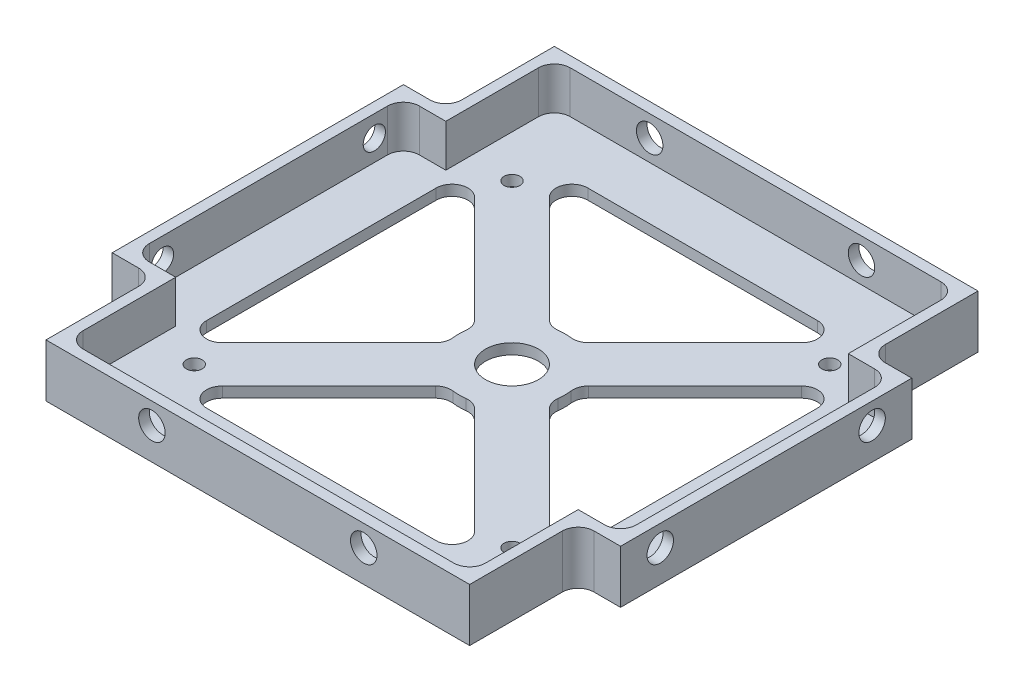
SolidWorks part; units mm, degrees
material "6061-T6 (SS)"
ref_plane "Front Plane" through (0, 0, 0) normal (0, 0, 1) x (1, 0, 0)
ref_plane "Top Plane" through (0, 0, 0) normal (0, 1, 0) x (1, 0, 0)
ref_plane "Right Plane" through (0, 0, 0) normal (1, 0, 0) x (0, 0, -1)
sketch "Sketch1" plane through (0, 0, 0) normal (0, 1, 0) x (1, 0, 0)
  line L0 (0, 8) -> (8, 0)
  line L1 (0, 0) -> (96, 0)
  line L2 (0, 0) -> (0, 96)
  line L3 (0, 96) -> (96, 96)
  line L4 (96, 0) -> (96, 96)
  line L5 (48, 96) -> (48, 0) construction
  line L6 (0, 48) -> (96, 48) construction
  line L7 (96, 8) -> (88, 0)
  line L8 (96, 88) -> (88, 96)
  line L9 (0, 88) -> (8, 96)
  dimension "D1" = 96
  dimension "D2" = 96
  dimension "D3" = 8
  dimension "D4" = 8
extrude "Boss-Extrude1" add sketch "Sketch1" along normal blind 10 contours L9 L2 L0 L1 L7 L4 L8 L3
sketch "Sketch2" plane through (0, 0, 0) normal (0, -1, 0) x (-1, 0, 0)
  line L0 (-4, 92) -> (-92, 4) construction
  line L1 (0, 88) -> (-8, 96) construction
  line L2 (-96, 8) -> (-88, 0) construction
  line L3 (-92, 92) -> (-4, 4) construction
  line L4 (-96, 88) -> (-88, 96) construction
  line L5 (0, 8) -> (-8, 0) construction
  line L6 (-12, 84) -> (-84, 84) construction
  line L7 (-84, 84) -> (-84, 12) construction
  line L8 (-84, 12) -> (-12, 12) construction
  line L9 (-12, 12) -> (-12, 84) construction
  line L10 (-8, 96) -> (-88, 96) construction
  line L12 (-19.0711, 84) -> (-84, 19.0711)
  line L13 (-12, 76.9289) -> (-76.9289, 12)
  line L14 (-12, 19.0711) -> (-76.9289, 84)
  line L15 (-19.0711, 12) -> (-84, 76.9289)
  line L16 (-12, 76.9289) -> (-12, 19.0711)
  line L17 (-19.0711, 12) -> (-76.9289, 12)
  line L18 (-84, 19.0711) -> (-84, 76.9289)
  line L19 (-76.9289, 84) -> (-19.0711, 84)
  circle A0 centre (-48, 48) radius 10
  circle A1 centre (-48, 48) radius 5
  dimension "D6" = 20
  dimension "D7" = 10
  dimension "D1" = 12
  dimension "D2" = 10
  dimension "D3" = 5
  dimension "D4" = 10
  dimension "D5" = 5
extrude "Cut-Extrude1" cut sketch "Sketch2" against normal through all contours A0 L12 L19 L14 | A0 L14 L16 L13 | A0 L13 L17 L15 | A0 L15 L18 L12 | A1
fillet "Fillet1" radius 3 16 edges at (19.0711, 5, -12) (76.9289, 5, -12) (50.5882, 5, -38.3407) (38.3407, 5, -50.5882) (45.4118, 5, -38.3407) (57.6593, 5, -50.5882) (12, 5, -19.0711) (38.3407, 5, -45.4118) (50.5882, 5, -57.6593) (84, 5, -19.0711) (84, 5, -76.9289) (57.6593, 5, -45.4118) (45.4118, 5, -57.6593) (76.9289, 5, -84) (19.0711, 5, -84) (12, 5, -76.9289)
sketch "Sketch5" plane through (0, 10, 0) normal (0, 1, 0) x (1, 0, 0)
  line L0 (8, 0) -> (8, 20.5)
  line L3 (0, 8) -> (8, 0)
  line L4 (0, 8) -> (0, 20.5)
  line L5 (0, 8) -> (0, 88) construction
  line L6 (0, 20.5) -> (8, 20.5)
  line L7 (0, 48) -> (96, 48) construction
  line L8 (96, 8) -> (96, 88) construction
  line L9 (48, 96) -> (48, 0) construction
  line L10 (8, 96) -> (88, 96) construction
  line L11 (8, 0) -> (88, 0) construction
  line L12 (96, 8) -> (88, 0)
  line L13 (96, 8) -> (96, 20.5)
  line L14 (96, 20.5) -> (88, 20.5)
  line L15 (88, 0) -> (88, 20.5)
  line L16 (96, 75.5) -> (88, 75.5)
  line L17 (96, 88) -> (96, 75.5)
  line L18 (96, 88) -> (88, 96)
  line L19 (88, 96) -> (88, 75.5)
  line L20 (8, 96) -> (8, 75.5)
  line L21 (0, 88) -> (8, 96)
  line L22 (0, 88) -> (0, 75.5)
  line L23 (0, 75.5) -> (8, 75.5)
  dimension "D1" = 20.5
extrude "Cut-Extrude4" cut sketch "Sketch5" against normal through all
sketch "Sketch6" plane through (0, 10, 0) normal (0, 1, 0) x (1, 0, 0)
  line L90 (86, 73.5) -> (86, 94)
  line L91 (94, 73.5) -> (86, 73.5)
  line L92 (94, 22.5) -> (94, 73.5)
  line L93 (86, 22.5) -> (94, 22.5)
  line L94 (86, 2) -> (86, 22.5)
  line L95 (10, 2) -> (86, 2)
  line L96 (10, 22.5) -> (10, 2)
  line L97 (2, 22.5) -> (10, 22.5)
  line L98 (2, 73.5) -> (2, 22.5)
  line L99 (10, 73.5) -> (2, 73.5)
  line L100 (10, 94) -> (10, 73.5)
  line L101 (86, 94) -> (10, 94)
  line L102 (86, 73.5) -> (86, 94)
  line L103 (94, 73.5) -> (86, 73.5)
  line L104 (94, 22.5) -> (94, 73.5)
  line L105 (86, 22.5) -> (94, 22.5)
  line L106 (86, 2) -> (86, 22.5)
  line L107 (10, 2) -> (86, 2)
  line L108 (10, 22.5) -> (10, 2)
  line L109 (2, 22.5) -> (10, 22.5)
  line L110 (2, 73.5) -> (2, 22.5)
  line L111 (10, 73.5) -> (2, 73.5)
  line L112 (10, 94) -> (10, 73.5)
  line L113 (86, 94) -> (10, 94)
  dimension "D1" = 2
extrude "Cut-Extrude5" cut sketch "Sketch6" against normal blind 8
fillet "Fillet2" radius 3 12 edges at (88, 5, -75.5) (88, 5, -20.5) (8, 5, -75.5) (8, 5, -20.5) (86, 6, -94) (94, 6, -73.5) (94, 6, -22.5) (86, 6, -2) (10, 6, -94) (10, 6, -2) (2, 6, -22.5) (2, 6, -73.5)
sketch "Sketch7" plane through (0, 0, 0) normal (0, -1, 0) x (1, 0, 0)
  line L0 (78, -18) -> (18, -18) construction
  line L1 (78, -78) -> (18, -78)
  line L2 (78, -78) -> (78, -18)
  line L3 (78, -18) -> (18, -18)
  line L4 (18, -78) -> (18, -18)
  line L5 (78, -78) -> (18, -18) construction
  line L6 (78, -18) -> (18, -78) construction
  line L7 (78, -18) -> (78, -78) construction
  line L8 (8, 0) -> (88, 0) construction
  line L9 (96, -20.5) -> (96, -75.5) construction
  line L10 (88, -96) -> (88, -78.5) construction
  circle A0 centre (78, -18) radius 1.5
  circle A1 centre (18, -18) radius 1.5
  circle A2 centre (18, -78) radius 1.5
  circle A3 centre (78, -78) radius 1.5
  point P0 (48, -48)
  dimension "D1" = 2
  dimension "D5" = 3
  dimension "D8" = 10
  dimension "D2" = 60
  dimension "D3" = 60
  dimension "D6" = 18
  dimension "D7" = 18
  dimension "D4" = 2
sketch "Sketch8" plane through (0, 0, 0) normal (0, 0, 1) x (1, 0, 0)
  line L0 (8, 6) -> (88, 6) construction
  line L1 (8, 10) -> (8, 0) construction
  line L2 (88, 10) -> (88, 0) construction
  line L3 (8, 0) -> (88, 0) construction
  line L4 (48, 10) -> (48, 0) construction
  line L5 (8, 10) -> (88, 10) construction
  dimension "D1" = 6
sketch "Sketch9" plane through (0, 0, 0) normal (-1, 0, 0) x (0, 0, 1)
  line L0 (-75.5, 6) -> (-20.5, 6) construction
  line L1 (-75.5, 0) -> (-75.5, 10) construction
  line L2 (-20.5, 0) -> (-20.5, 10) construction
  line L3 (-20.5, 0) -> (-75.5, 0) construction
  line L4 (-48, 10) -> (-48, 0) construction
  line L5 (-20.5, 10) -> (-75.5, 10) construction
  dimension "D1" = 6
hole_wizard "Ø5.0mm Dowel Hole2" positions "Sketch12" profile "Sketch13" hole size "Ø5.0" standard "ANSI Metric"
sketch "Sketch12" plane through (0, 0, 0) normal (0, 0, 1) x (1, 0, 0)
  line L0 (8, 6) -> (88, 6) construction
  line L2 (48, 10) -> (48, 0) construction
  point P0 (28, 6)
  point P4 (68, 6)
  dimension "D1" = 40
  dimension "D2" = 20
sketch "Sketch13" plane through (28, 6, 0) normal (1, 0, 0) x (0, -1, 0)
  line L0 (0, 0) -> (0, 9.0022)
  line L1 (0, 9.0022) -> (2.5, 7.5)
  line L2 (2.5, 7.5) -> (2.5, 0)
  line L5 (2.5, 0) -> (0, 0)
  line L10 (0, 9.0022) -> (-2.5, 7.5) construction
  line L11 (0, -6.35) -> (0, 107.95) construction
  dimension "Hole Dia." = 5
  dimension "Hole Depth" = 7.5
  dimension "Drill Angle" = 118
hole_wizard "Tap Drill for M5x0.8 Tap1" positions "Sketch14" profile "Sketch15" hole size "M5x0.8" standard "ANSI Metric" end condition up to next
sketch "Sketch14" plane through (0, 0, 0) normal (-1, 0, 0) x (0, 0, 1)
  line L0 (-75.5, 6) -> (-20.5, 6) construction
  line L1 (-48, 10) -> (-48, 0) construction
  point P0 (-68, 6)
  point P4 (-28, 6)
  dimension "D1" = 40
  dimension "D2" = 20
sketch "Sketch15" plane through (0, 6, -68) normal (0, 1, 0) x (0, 0, 1)
  line L0 (0, 0) -> (0, 2)
  line L1 (0, 2) -> (2.1, 2)
  line L2 (2.1, 2) -> (2.1, 0)
  line L5 (2.1, 0) -> (0, 0)
  line L11 (0, -6.35) -> (0, 107.95) construction
  dimension "Thru Hole Dia." = 4.2
  dimension "Thru Hole Depth" = 2
ref_plane "Plane1" through (48, 0, 0) normal (-1, 0, 0) x (0, 0, 1)
ref_plane "Plane2" through (0, 0, -48) normal (0, 0, 1) x (1, 0, 0)
mirror "Mirror1" about plane through (0, 0, -48) normal (0, 0, 1) of "Ø5.0mm Dowel Hole2"
sketch "Sketch16" plane through (0, 0, 0) normal (-1, 0, 0) x (0, 0, 1)
  line L0 (-48, 0) -> (-48, 10) construction
  line L1 (-20.5, 0) -> (-75.5, 0) construction
  line L2 (-20.5, 10) -> (-75.5, 10) construction
  line L4 (-40.9661, 4.5188) -> (-54.475, 4.5188) construction
hole_wizard "Ø3.0mm Dowel Hole3" positions "3DSketch1" profile "Sketch17" hole size "Ø3.0" standard "ANSI Metric" end condition through all
sketch3d "3DSketch1"
  point P0 (78, 0, -18)
  point P3 (78, 0, -78)
  point P6 (18, 0, -78)
  point P9 (18, 0, -18)
sketch "Sketch17" plane through (78, 0, -18) normal (1, 0, 0) x (0, 0, -1)
  line L0 (0, 0) -> (0, 10)
  line L1 (0, 10) -> (1.5, 10)
  line L2 (1.5, 10) -> (1.5, 0)
  line L5 (1.5, 0) -> (0, 0)
  line L11 (0, -6.35) -> (0, 107.95) construction
  dimension "Thru Hole Dia." = 3
  dimension "Thru Hole Depth" = 10
sketch "Sketch18" plane through (96, 0, 0) normal (1, 0, 0) x (0, 0, -1)
  line L1 (20.5, 0) -> (75.5, 0) construction
  line L4 (75.5, 0) -> (75.5, 10) construction
  point P8 (28, 6)
  point P9 (68, 6)
  dimension "D1" = 7.5
  dimension "D2" = 6
  dimension "D3" = 40
  dimension "D4" = 6
hole_wizard "Ø5.0mm Dowel Hole1" positions "3DSketch2" profile "Sketch19" hole size "Ø5.0" standard "ANSI Metric" end condition up to next
sketch3d "3DSketch2"
  point P0 (96, 6, -68)
  point P3 (96, 6, -28)
sketch "Sketch19" plane through (96, 6, -68) normal (0, 1, 0) x (0, 0, -1)
  line L0 (0, 0) -> (0, 2)
  line L1 (0, 2) -> (2.5, 2)
  line L2 (2.5, 2) -> (2.5, 0)
  line L5 (2.5, 0) -> (0, 0)
  line L11 (0, -6.35) -> (0, 107.95) construction
  dimension "Thru Hole Dia." = 5
  dimension "Thru Hole Depth" = 2
